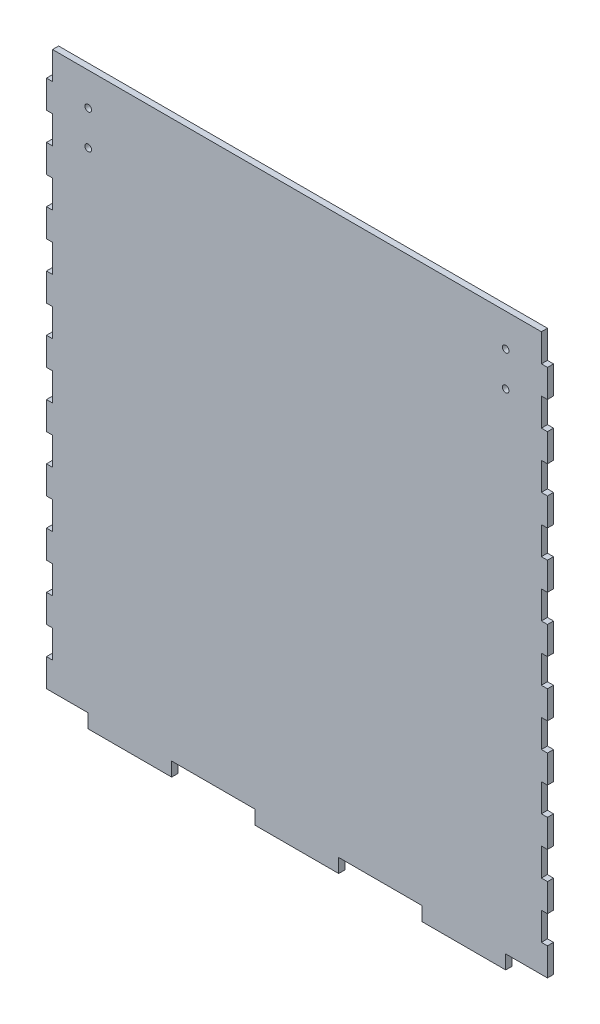
SolidWorks part; units mm, degrees
material "Acrylic (Medium-high impact)"
ref_plane "Front Plane" through (0, 0, 0) normal (0, 0, 1) x (1, 0, 0)
ref_plane "Top Plane" through (0, 0, 0) normal (0, 1, 0) x (1, 0, 0)
ref_plane "Right Plane" through (0, 0, 0) normal (1, 0, 0) x (0, 0, -1)
sketch "Sketch1" plane through (0, 0, 0) normal (0, 0, 1) x (1, 0, 0)
  line L0 (-114.3, 114.3) -> (-111.5219, 114.3)
  line L1 (-114.3, 127) -> (114.3, 127)
  line L2 (-114.3, 127) -> (-114.3, -127)
  line L3 (-114.3, -127) -> (114.3, -127)
  line L4 (114.3, 127) -> (114.3, -127)
  line L5 (-114.3, 127) -> (-111.5219, 127)
  line L6 (-114.3, 127) -> (-114.3, 114.3)
  line L7 (-114.3, 114.3) -> (-111.5219, 114.3)
  line L8 (-111.5219, 127) -> (-111.5219, 114.3)
  line L9 (-114.3, 114.3) -> (-114.3, 101.6)
  line L10 (-114.3, 101.6) -> (-111.5219, 101.6)
  line L11 (-111.5219, 114.3) -> (-111.5219, 101.6)
  line L12 (-114.3, 101.6) -> (-111.5219, 101.6)
  line L13 (-114.3, 101.6) -> (-114.3, 88.9)
  line L14 (-114.3, 88.9) -> (-111.5219, 88.9)
  line L15 (-111.5219, 101.6) -> (-111.5219, 88.9)
  line L16 (-114.3, 88.9) -> (-111.5219, 88.9)
  line L17 (-114.3, 88.9) -> (-114.3, 76.2)
  line L18 (-114.3, 76.2) -> (-111.5219, 76.2)
  line L19 (-111.5219, 88.9) -> (-111.5219, 76.2)
  line L20 (-114.3, 76.2) -> (-111.5219, 76.2)
  line L21 (-114.3, 76.2) -> (-114.3, 63.5)
  line L22 (-114.3, 63.5) -> (-111.5219, 63.5)
  line L23 (-111.5219, 76.2) -> (-111.5219, 63.5)
  line L24 (-114.3, 63.5) -> (-111.5219, 63.5)
  line L25 (-114.3, 63.5) -> (-114.3, 50.8)
  line L26 (-114.3, 50.8) -> (-111.5219, 50.8)
  line L27 (-111.5219, 63.5) -> (-111.5219, 50.8)
  line L28 (-114.3, 50.8) -> (-111.5219, 50.8)
  line L29 (-114.3, 50.8) -> (-114.3, 38.1)
  line L30 (-114.3, 38.1) -> (-111.5219, 38.1)
  line L31 (-111.5219, 50.8) -> (-111.5219, 38.1)
  line L32 (-114.3, 38.1) -> (-111.5219, 38.1)
  line L33 (-114.3, 38.1) -> (-114.3, 25.4)
  line L34 (-114.3, 25.4) -> (-111.5219, 25.4)
  line L35 (-111.5219, 38.1) -> (-111.5219, 25.4)
  line L36 (-114.3, 25.4) -> (-111.5219, 25.4)
  line L37 (-114.3, 25.4) -> (-114.3, 12.7)
  line L38 (-114.3, 12.7) -> (-111.5219, 12.7)
  line L39 (-111.5219, 25.4) -> (-111.5219, 12.7)
  line L40 (-114.3, 12.7) -> (-111.5219, 12.7)
  line L41 (-114.3, 12.7) -> (-114.3, 0)
  line L42 (-114.3, 0) -> (-111.5219, 0)
  line L43 (-111.5219, 12.7) -> (-111.5219, 0)
  line L44 (-114.3, 0) -> (-111.5219, 0)
  line L45 (-114.3, 0) -> (-114.3, -12.7)
  line L46 (-114.3, -12.7) -> (-111.5219, -12.7)
  line L47 (-111.5219, 0) -> (-111.5219, -12.7)
  line L48 (-114.3, -12.7) -> (-111.5219, -12.7)
  line L49 (-114.3, -12.7) -> (-114.3, -25.4)
  line L50 (-114.3, -25.4) -> (-111.5219, -25.4)
  line L51 (-111.5219, -12.7) -> (-111.5219, -25.4)
  line L52 (-114.3, -25.4) -> (-111.5219, -25.4)
  line L53 (-114.3, -25.4) -> (-114.3, -38.1)
  line L54 (-114.3, -38.1) -> (-111.5219, -38.1)
  line L55 (-111.5219, -25.4) -> (-111.5219, -38.1)
  line L56 (-114.3, -38.1) -> (-111.5219, -38.1)
  line L57 (-114.3, -38.1) -> (-114.3, -50.8)
  line L58 (-114.3, -50.8) -> (-111.5219, -50.8)
  line L59 (-111.5219, -38.1) -> (-111.5219, -50.8)
  line L60 (-114.3, -50.8) -> (-111.5219, -50.8)
  line L61 (-114.3, -50.8) -> (-114.3, -63.5)
  line L62 (-114.3, -63.5) -> (-111.5219, -63.5)
  line L63 (-111.5219, -50.8) -> (-111.5219, -63.5)
  line L64 (-114.3, -63.5) -> (-111.5219, -63.5)
  line L65 (-114.3, -63.5) -> (-114.3, -76.2)
  line L66 (-114.3, -76.2) -> (-111.5219, -76.2)
  line L67 (-111.5219, -63.5) -> (-111.5219, -76.2)
  line L68 (-114.3, -76.2) -> (-111.5219, -76.2)
  line L69 (-114.3, -76.2) -> (-114.3, -88.9)
  line L70 (-114.3, -88.9) -> (-111.5219, -88.9)
  line L71 (-111.5219, -76.2) -> (-111.5219, -88.9)
  line L72 (-114.3, -88.9) -> (-111.5219, -88.9)
  line L73 (-114.3, -88.9) -> (-114.3, -101.6)
  line L74 (-114.3, -101.6) -> (-111.5219, -101.6)
  line L75 (-111.5219, -88.9) -> (-111.5219, -101.6)
  line L76 (-114.3, -101.6) -> (-111.5219, -101.6)
  line L77 (-114.3, -101.6) -> (-114.3, -114.3)
  line L78 (-114.3, -114.3) -> (-111.5219, -114.3)
  line L79 (-111.5219, -101.6) -> (-111.5219, -114.3)
  line L80 (-114.3, -114.3) -> (-111.5219, -114.3)
  line L81 (-114.3, -114.3) -> (-114.3, -127)
  line L82 (-114.3, -127) -> (-111.5219, -127)
  line L83 (-111.5219, -114.3) -> (-111.5219, -127)
  line L100 (0, 127) -> (0, -127) construction
  line L101 (114.3, 114.3) -> (111.5219, 114.3)
  line L102 (114.3, 127) -> (111.5219, 127)
  line L103 (114.3, 127) -> (114.3, 114.3)
  line L104 (114.3, 114.3) -> (111.5219, 114.3)
  line L105 (111.5219, 127) -> (111.5219, 114.3)
  line L106 (114.3, 114.3) -> (114.3, 101.6)
  line L107 (114.3, 101.6) -> (111.5219, 101.6)
  line L108 (111.5219, 114.3) -> (111.5219, 101.6)
  line L109 (114.3, 101.6) -> (111.5219, 101.6)
  line L110 (114.3, 101.6) -> (114.3, 88.9)
  line L111 (114.3, 88.9) -> (111.5219, 88.9)
  line L112 (111.5219, 101.6) -> (111.5219, 88.9)
  line L113 (114.3, 88.9) -> (111.5219, 88.9)
  line L114 (114.3, 88.9) -> (114.3, 76.2)
  line L115 (114.3, 76.2) -> (111.5219, 76.2)
  line L116 (111.5219, 88.9) -> (111.5219, 76.2)
  line L117 (114.3, 76.2) -> (111.5219, 76.2)
  line L118 (114.3, 76.2) -> (114.3, 63.5)
  line L119 (114.3, 63.5) -> (111.5219, 63.5)
  line L120 (111.5219, 76.2) -> (111.5219, 63.5)
  line L121 (114.3, 63.5) -> (111.5219, 63.5)
  line L122 (114.3, 63.5) -> (114.3, 50.8)
  line L123 (114.3, 50.8) -> (111.5219, 50.8)
  line L124 (111.5219, 63.5) -> (111.5219, 50.8)
  line L125 (114.3, 50.8) -> (111.5219, 50.8)
  line L126 (114.3, 50.8) -> (114.3, 38.1)
  line L127 (114.3, 38.1) -> (111.5219, 38.1)
  line L128 (111.5219, 50.8) -> (111.5219, 38.1)
  line L129 (114.3, 38.1) -> (111.5219, 38.1)
  line L130 (114.3, 38.1) -> (114.3, 25.4)
  line L131 (114.3, 25.4) -> (111.5219, 25.4)
  line L132 (111.5219, 38.1) -> (111.5219, 25.4)
  line L133 (114.3, 25.4) -> (111.5219, 25.4)
  line L134 (114.3, 25.4) -> (114.3, 12.7)
  line L135 (114.3, 12.7) -> (111.5219, 12.7)
  line L136 (111.5219, 25.4) -> (111.5219, 12.7)
  line L137 (114.3, 12.7) -> (111.5219, 12.7)
  line L138 (114.3, 12.7) -> (114.3, 0)
  line L139 (114.3, 0) -> (111.5219, 0)
  line L140 (111.5219, 12.7) -> (111.5219, 0)
  line L141 (114.3, 0) -> (111.5219, 0)
  line L142 (114.3, 0) -> (114.3, -12.7)
  line L143 (114.3, -12.7) -> (111.5219, -12.7)
  line L144 (111.5219, 0) -> (111.5219, -12.7)
  line L145 (114.3, -12.7) -> (111.5219, -12.7)
  line L146 (114.3, -12.7) -> (114.3, -25.4)
  line L147 (114.3, -25.4) -> (111.5219, -25.4)
  line L148 (111.5219, -12.7) -> (111.5219, -25.4)
  line L149 (114.3, -25.4) -> (111.5219, -25.4)
  line L150 (114.3, -25.4) -> (114.3, -38.1)
  line L151 (114.3, -38.1) -> (111.5219, -38.1)
  line L152 (111.5219, -25.4) -> (111.5219, -38.1)
  line L153 (114.3, -38.1) -> (111.5219, -38.1)
  line L154 (114.3, -38.1) -> (114.3, -50.8)
  line L155 (114.3, -50.8) -> (111.5219, -50.8)
  line L156 (111.5219, -38.1) -> (111.5219, -50.8)
  line L157 (114.3, -50.8) -> (111.5219, -50.8)
  line L158 (114.3, -50.8) -> (114.3, -63.5)
  line L159 (114.3, -63.5) -> (111.5219, -63.5)
  line L160 (111.5219, -50.8) -> (111.5219, -63.5)
  line L161 (114.3, -63.5) -> (111.5219, -63.5)
  line L162 (114.3, -63.5) -> (114.3, -76.2)
  line L163 (114.3, -76.2) -> (111.5219, -76.2)
  line L164 (111.5219, -63.5) -> (111.5219, -76.2)
  line L165 (114.3, -76.2) -> (111.5219, -76.2)
  line L166 (114.3, -76.2) -> (114.3, -88.9)
  line L167 (114.3, -88.9) -> (111.5219, -88.9)
  line L168 (111.5219, -76.2) -> (111.5219, -88.9)
  line L169 (114.3, -88.9) -> (111.5219, -88.9)
  line L170 (114.3, -88.9) -> (114.3, -101.6)
  line L171 (114.3, -101.6) -> (111.5219, -101.6)
  line L172 (111.5219, -88.9) -> (111.5219, -101.6)
  line L173 (114.3, -101.6) -> (111.5219, -101.6)
  line L174 (114.3, -101.6) -> (114.3, -114.3)
  line L175 (114.3, -114.3) -> (111.5219, -114.3)
  line L176 (111.5219, -101.6) -> (111.5219, -114.3)
  line L177 (114.3, -114.3) -> (111.5219, -114.3)
  line L178 (114.3, -114.3) -> (114.3, -127)
  line L179 (114.3, -127) -> (111.5219, -127)
  line L180 (111.5219, -114.3) -> (111.5219, -127)
  line L186 (95.25, -127) -> (95.25, -133.35)
  line L187 (95.25, -133.35) -> (57.15, -133.35)
  line L188 (57.15, -133.35) -> (57.15, -127)
  line L189 (57.15, -127) -> (95.25, -127)
  line L191 (-19.05, -127) -> (19.05, -127)
  line L192 (19.05, -127) -> (19.05, -133.35)
  line L193 (19.05, -133.35) -> (-19.05, -133.35)
  line L194 (-19.05, -133.35) -> (-19.05, -127)
  line L195 (-95.25, -127) -> (-57.15, -127)
  line L196 (-57.15, -127) -> (-57.15, -133.35)
  line L197 (-57.15, -133.35) -> (-95.25, -133.35)
  line L198 (-95.25, -133.35) -> (-95.25, -127)
  point P4 (0, 127)
  point P6 (-114.3, 0)
  dimension "D1" = 254
  dimension "D2" = 228.6
  dimension "D3" = 12.7
  dimension "D4" = 2.7781
  dimension "D7" = 6.35
  dimension "D8" = 38.1
  dimension "D9" = 19.05
  dimension "D5" = 20
  dimension "D6" = 20
  dimension "D10" = 3
extrude "Boss-Extrude1" add sketch "Sketch1" along normal blind 2.7781
sketch "Sketch2" plane through (0, 0, 2.7781) normal (0, 0, 1) x (1, 0, 0)
  line L0 (-25.4, -88.9) -> (25.4, -88.9) construction
  line L1 (0, -85.725) -> (0, -114.3) construction
  line L2 (-15.5, -85.725) -> (15.5, -85.725)
  line L3 (-15.5, -85.725) -> (-15.5, -114.3)
  line L5 (95.25, -127) -> (114.3, -127) construction
  line L8 (-15.5, -114.3) -> (15.5, -114.3)
  line L9 (15.5, -85.725) -> (15.5, -114.3)
  line L12 (-114.3, -114.3) -> (-114.3, -127) construction
  circle A0 centre (-25.4, -88.9) radius 1.5
  circle A1 centre (25.4, -88.9) radius 1.5
  point P12 (0, -88.9)
  dimension "D1" = 3
  dimension "D2" = 50.8
  dimension "D3" = 31
  dimension "D4" = 25.4
  dimension "D5" = 28.575
  dimension "D6" = 12.7
  dimension "D7" = 114.3
extrude "Cut-Extrude1" [suppressed] cut sketch "Sketch2" against normal through all
sketch "Sketch3" plane through (0, 0, 0) normal (0, 0, -1) x (-1, 0, 0)
  line L0 (-114.3, 114.3) -> (-114.3, 101.6) construction
  line L1 (111.5219, 127) -> (-111.5219, 127) construction
  line L2 (0, 127) -> (0, -133.35) construction
  line L3 (-19.05, -133.35) -> (19.05, -133.35) construction
  circle A0 centre (-95.25, 112) radius 1.5
  circle A1 centre (-95.25, 96.25) radius 1.5
  circle A2 centre (95.25, 96.25) radius 1.5
  circle A3 centre (95.25, 112) radius 1.5
  dimension "D1" = 3
  dimension "D2" = 3
  dimension "D3" = 15.75
  dimension "D4" = 19.05
  dimension "D5" = 15
extrude "Cut-Extrude2" cut sketch "Sketch3" against normal up to surface (2.7781 mm away) up to face at (0, -16.9793, 2.7781)
equation "\"wall_thickness\" = 7/64in"
equation "\"base_thickness\" = 0.25in"
equation "\"D4@Sketch1\"=\"wall_thickness\""
equation "\"D7@Sketch1\"=\"base_thickness\""
equation "\"D1@Boss-Extrude1\"=\"wall_thickness\""
